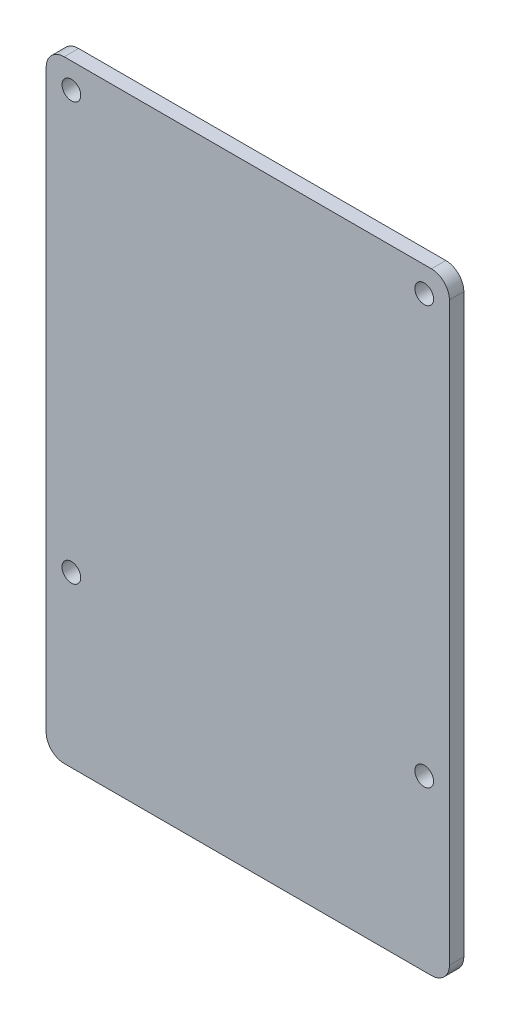
SolidWorks part; units mm, degrees
ref_plane "前视基准面" through (0, 0, 0) normal (0, 0, 1) x (1, 0, 0)
ref_plane "上视基准面" through (0, 0, 0) normal (0, 1, 0) x (1, 0, 0)
ref_plane "右视基准面" through (0, 0, 0) normal (1, 0, 0) x (0, 0, -1)
sketch "草图1" plane through (0, 0, 0) normal (0, 0, 1) x (1, 0, 0)
  line L2 (-1, 3.5) -> (50, 3.5)
  line L3 (-3.5, 1) -> (-3.5, -79)
  line L4 (-1, -81.5) -> (50, -81.5)
  line L5 (52.5, 1) -> (52.5, -79)
  line L7 (-1, 3.5) -> (50, 3.5) construction
  line L8 (0, 0) -> (49, 0) construction
  line L9 (24.5, 3.5) -> (24.5, -81.5) construction
  circle A0 centre (49, 0) radius 1.3
  circle A1 centre (49, -58) radius 1.3
  circle A2 centre (0, -58) radius 1.3
  circle A3 centre (0, 0) radius 1.3
  arc A4 (-3.5, -79) -> (-1, -81.5) centre (-1, -79) ccw
  arc A5 (50, -81.5) -> (52.5, -79) centre (50, -79) ccw
  arc A6 (50, 3.5) -> (52.5, 1) centre (50, 1) cw
  arc A7 (-1, 3.5) -> (-3.5, 1) centre (-1, 1) ccw
  point P14 (24.5, 0)
  point P25 (52.5, -81.5)
  point P28 (52.5, 3.5)
  point P31 (-3.5, 3.5)
  dimension "D4" = 2.6
  dimension "D5" = 2.6
  dimension "D6" = 2.5
  dimension "D1" = 56
  dimension "D2" = 85
  dimension "D3" = 0
extrude "凸台-拉伸1" add sketch "草图1" along normal blind 2
